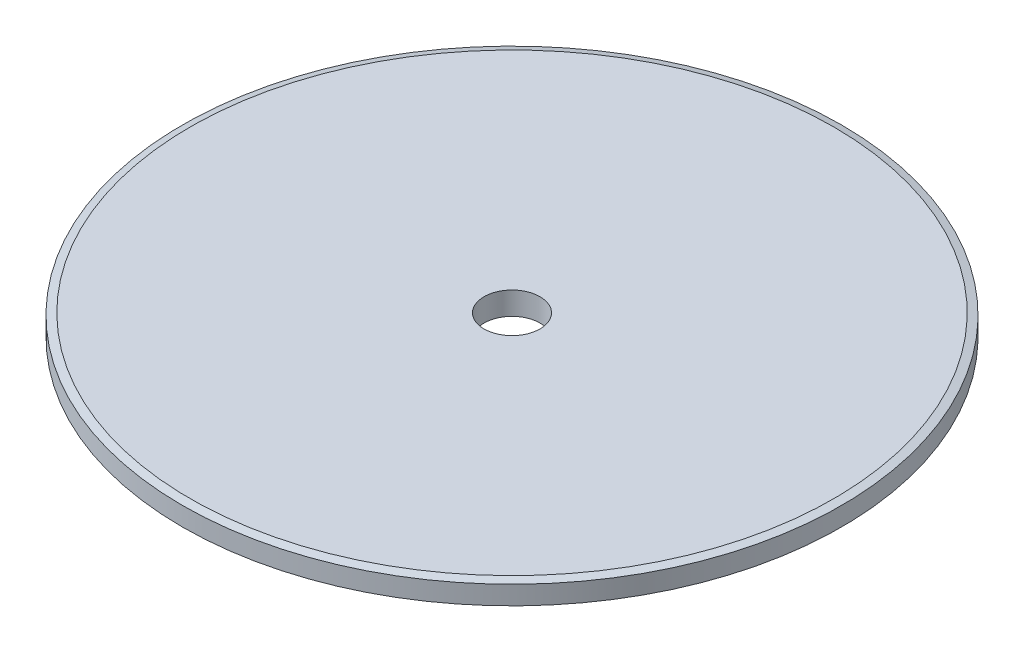
SolidWorks part; units mm, degrees
material "Сталь ШХ15 ГОСТ 801-78"
ref_plane "Plane1" through (0, 0, 0) normal (0, 0, 1) x (1, 0, 0)
ref_plane "Plane2" through (0, 0, 0) normal (0, 1, 0) x (1, 0, 0)
ref_plane "Plane3" through (0, 0, 0) normal (1, 0, 0) x (0, 0, -1)
sketch "Эскиз1" plane through (0, 0, 0) normal (0, 0, 1) x (1, 0, 0)
  line L0 (0, 0) -> (70.7, 0)
  line L1 (70.7, 0) -> (70.7, 4.9)
  line L2 (70.7, 4.9) -> (0, 4.9)
  line L5 (0, 4.9) -> (0, 0)
  point P3 (12, 4.9)
  point P6 (0.1767, 4.9)
  dimension "D1" = 4.9
  dimension "30" = 70.7
ref_axis "Ось1" through (0, 4.9, 0) along (0, -1, 0)
revolve "Повернуть2" add sketch "Эскиз1" angle 360 about axis through (0, 4.9, 0) along (0, -1, 0)
chamfer "Фаска1" distance 1.645 angle 15 1 edges at (0, 4.9, 70.7)
chamfer "Фаска2" distance 1.645 angle 15 1 edges at (0, 0, 70.7)
sketch "Эскиз2" plane through (0, 0, 0) normal (0, -1, 0) x (-1, 0, 0)
  circle A0 centre (0, 0) radius 6
  dimension "D1" = 12
extrude "Вырез-Вытянуть3" cut sketch "Эскиз2" against normal through all both contours A0
